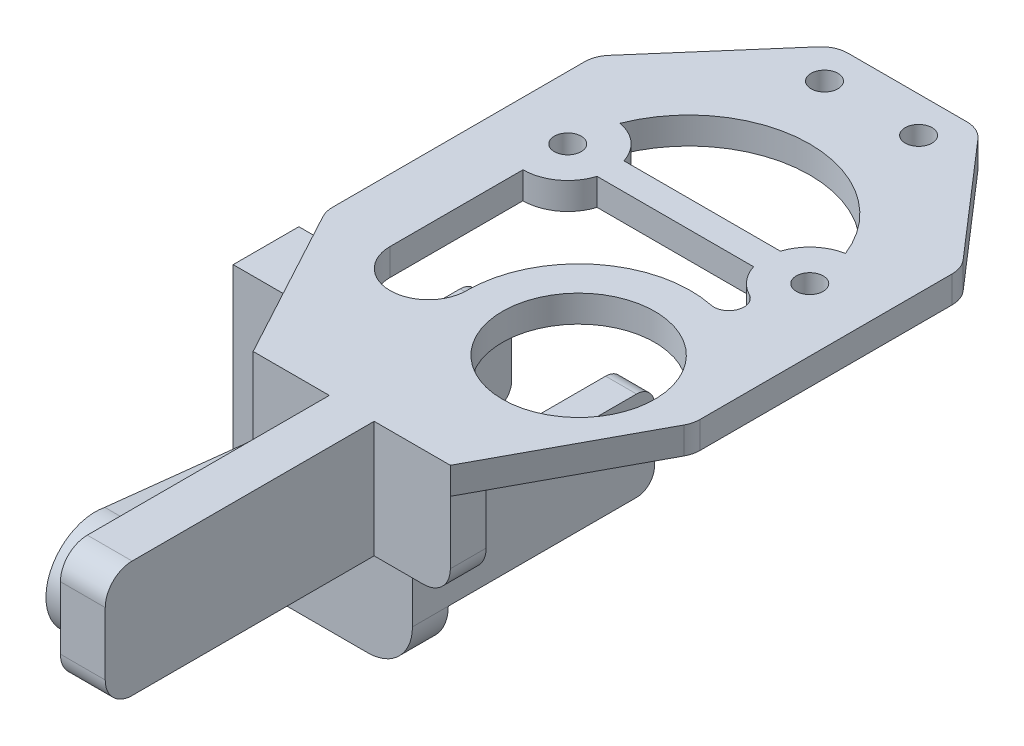
SolidWorks part; units mm, degrees
ref_plane "Front" through (0, 0, 0) normal (0, 0, 1) x (1, 0, 0)
ref_plane "Top" through (0, 0, 0) normal (0, 1, 0) x (1, 0, 0)
ref_plane "Right" through (0, 0, 0) normal (1, 0, 0) x (0, 0, -1)
sketch "Sketch1" plane through (0, 0, 0) normal (0, 1, 0) x (1, 0, 0)
  line L0 (0, 24.4003) -> (0, 0) construction
  line L1 (0, 0) -> (-13.5, 0) construction
  line L2 (8, 24.4003) -> (-8, 24.4003)
  line L3 (-8, 24.4003) -> (-20.5, 10)
  line L4 (-20.5, 10) -> (-20.5, -20)
  line L5 (-20.5, -20) -> (-11, -37.5997)
  line L6 (-11, -37.5997) -> (11, -37.5997)
  line L7 (20.5, -20) -> (11, -37.5997)
  line L8 (20.5, 10) -> (20.5, -20)
  line L9 (8, 24.4003) -> (20.5, 10)
  line L11 (7.5302, -19.8174) -> (17.65, -25.2799) construction
  line L12 (-13.5, -5) -> (-13.5, -19.8174)
  line L13 (8.7303, -1.5) -> (-8.7303, -1.5)
  line L15 (8.7303, 1.5) -> (-8.7303, 1.5)
  line L17 (8.7303, -1.5) -> (-8.7303, 1.5) construction
  line L18 (8.7303, 1.5) -> (-8.7303, -1.5) construction
  arc A0 (12.5741, 4.9135) -> (-12.5741, 4.9135) centre (0, 0) ccw
  circle A1 centre (-5.25, 20.3945) radius 1.5
  circle A4 centre (5.25, 20.3945) radius 1.5
  arc A5 (-13.5, -5) -> (-8.7303, -1.5) centre (-13.5, 0) ccw
  arc A6 (8.7303, -1.5) -> (11.188, -4.4333) centre (13.5, 0) ccw
  circle A7 centre (-13.5, 0) radius 1.5
  circle A8 centre (13.5, 0) radius 1.5
  arc A9 (-13.5, -19.8174) -> (-4.9698, -19.8174) centre (-9.2349, -19.8174) ccw
  arc A10 (-4.9698, -19.8174) -> (10.0668, -7.5775) centre (7.5302, -19.8174) cw
  arc A11 (10.0668, -7.5775) -> (11.188, -4.4333) centre (10.4088, -5.9275) ccw
  circle A12 centre (7.5302, -19.8174) radius 8.5
  arc A13 (-8.7303, 1.5) -> (-12.5741, 4.9135) centre (-13.5, 0) ccw
  arc A14 (12.5741, 4.9135) -> (8.7303, 1.5) centre (13.5, 0) ccw
  point P15 (0, -37.5997)
  dimension "D7" = 10.5
  dimension "D8" = 3
  dimension "D10" = 17
  dimension "D15" = 4
  dimension "D16" = 10
  dimension "D17" = 13.5
  dimension "D18" = 3
  dimension "D19" = 3
  dimension "D24" = 22
  dimension "D1" = 62
  dimension "D2" = 41
  dimension "D3" = 16
  dimension "D4" = 22
  dimension "D9" = 11.5
  dimension "D11" = 6
  dimension "D12" = 20
  dimension "D13" = 30
  dimension "D14" = 10
  dimension "D20" = 3
  dimension "D21" = 45
  dimension "D22" = 13.5
extrude "Boss-Extrude1" add sketch "Sketch1" along normal mid plane 3
fillet "Fillet1" radius 3 6 edges at (-20.5, 0, 20) (-20.5, 0, -10) (-8, 0, -24.4003) (8, 0, -24.4003) (20.5, 0, -10) (20.5, 0, 20)
sketch "Sketch4" plane through (0, -1.5, 0) normal (0, -1, 0) x (1, 0, 0)
  line L0 (-13.5, 1.5) -> (-13.5, 25.3259)
  line L2 (-23.5, 23.3259) -> (-3.5, 23.3259)
  line L3 (-23.5, 23.3259) -> (-23.5, 27.3259)
  line L4 (-23.5, 27.3259) -> (-3.5, 27.3259)
  line L5 (-3.5, 23.3259) -> (-3.5, 27.3259)
  line L6 (-23.5, 23.3259) -> (-3.5, 27.3259) construction
  line L7 (-23.5, 27.3259) -> (-3.5, 23.3259) construction
  circle A0 centre (-13.5, 0) radius 1.5 construction
  dimension "D1" = 20
  dimension "D2" = 4
extrude "Boss-Extrude2" add sketch "Sketch4" along normal blind 30
sketch "Sketch5" plane through (0, 0, 23.3259) normal (0, 0, -1) x (-1, 0, 0)
  line L0 (23.5, -31.5) -> (11.6601, -31.5) construction
  line L1 (11.6601, -1.5) -> (14.7975, -1.5)
  line L2 (11.6601, -1.5) -> (11.6601, -31.5)
  line L3 (11.6601, -31.5) -> (14.7975, -31.5)
sketch "Sketch7" plane through (0, -1.5, 0) normal (0, -1, 0) x (1, 0, 0)
  line L0 (-13.5, 0) -> (-7.25, 0)
  line L1 (-13.5, 0) -> (-19.75, 0)
  line L2 (-6.8097, 23.3259) -> (-3.5, 23.3259) construction
  line L3 (-7.25, 0) -> (-3.5, 0)
  line L4 (-7.25, 0) -> (-7.25, 23.3259)
  line L5 (-7.25, 23.3259) -> (-3.5, 23.3259)
  line L6 (-3.5, 0) -> (-3.5, 23.3259)
  line L8 (-19.75, 0) -> (-23.5, 0)
  line L9 (-19.75, 0) -> (-19.75, 23.3259)
  line L10 (-19.75, 23.3259) -> (-23.5, 23.3259)
  line L11 (-23.5, 0) -> (-23.5, 23.3259)
extrude "Boss-Extrude4" add sketch "Sketch7" along normal blind 25 contours L9 L8 L11 L10
sketch "Sketch10" plane through (0, 0, 23.3259) normal (0, 0, -1) x (-1, 0, 0)
  line L1 (3.5, -1.5) -> (6.95, -1.5)
  line L2 (3.5, -1.5) -> (3.5, -26.5)
  line L3 (3.5, -26.5) -> (6.95, -26.5)
  line L4 (6.95, -1.5) -> (6.95, -26.5)
  dimension "D1" = 3.45
  dimension "D2" = 25
extrude "Boss-Extrude15" add sketch "Sketch10" along normal blind 23
sketch "Sketch11" plane through (0, 0, 0) normal (0, 0, -1) x (-1, 0, 0)
  line L0 (19.75, -26.5) -> (19.75, -1.5) construction
  line L1 (23.5, -1.5) -> (19.75, -1.5)
  line L2 (23.5, -1.5) -> (23.5, -16.5)
  line L3 (23.5, -16.5) -> (19.75, -16.5)
  line L4 (19.75, -1.5) -> (19.75, -16.5)
  dimension "D1" = 15
extrude "Cut-Extrude1" cut sketch "Sketch11" against normal blind 20
sketch "Sketch12" plane through (0, 0, 0.3259) normal (0, 0, -1) x (-1, 0, 0)
  line L0 (3.5, -1.5) -> (3.5, -26.5) construction
  line L1 (6.95, -1.5) -> (3.5, -1.5)
  line L2 (6.95, -1.5) -> (6.95, -16.5)
  line L3 (6.95, -16.5) -> (3.5, -16.5)
  line L4 (3.5, -1.5) -> (3.5, -16.5)
  dimension "D1" = 15
extrude "Cut-Extrude2" cut sketch "Sketch12" against normal blind 20
sketch "Sketch13" plane through (0, -1.5, 0) normal (0, -1, 0) x (1, 0, 0)
  line L1 (11, 37.5997) -> (-11, 37.5997)
  line L2 (11, 37.5997) -> (11, 33.5997)
  line L3 (11, 33.5997) -> (-11, 33.5997)
  line L4 (-11, 37.5997) -> (-11, 33.5997)
  dimension "D1" = 4
extrude "Boss-Extrude16" add sketch "Sketch13" along normal blind 10
sketch "Sketch14" plane through (0, 0, 37.5997) normal (0, 0, 1) x (1, 0, 0)
  line L0 (0, -11.5) -> (0, 1.5)
  line L1 (11, -11.5) -> (-11, -11.5) construction
  line L2 (-11, 1.5) -> (11, 1.5) construction
  line L4 (-2.5, 1.5) -> (2.5, 1.5)
  line L5 (-2.5, 1.5) -> (-2.5, -11.5)
  line L6 (-2.5, -11.5) -> (2.5, -11.5)
  line L7 (2.5, 1.5) -> (2.5, -11.5)
  line L8 (-2.5, 1.5) -> (2.5, -11.5) construction
  line L9 (-2.5, -11.5) -> (2.5, 1.5) construction
  point P6 (0, -5)
  line M7 (-11, -11.5) -> (11, -11.5)
  line M10 (11, 1.5) -> (-11, 1.5)
  dimension "D1" = 5
extrude "Boss-Extrude17" add sketch "Sketch14" along normal blind 30 contours L7 L0 M10 M7 | L5 L0 M10 M7
fillet "Fillet3" radius 3 1 edges at (-11, -11.5, 35.5997)
fillet "Fillet4" radius 3 1 edges at (11, -11.5, 35.5997)
fillet "Fillet5" radius 3 1 edges at (0, 1.5, 67.5997)
fillet "Fillet6" radius 3 1 edges at (0, -11.5, 67.5997)
fillet "Fillet7" radius 2 1 edges at (-21.625, -16.5, 0)
fillet "Fillet8" radius 2 1 edges at (-21.625, -26.5, 0)
fillet "Fillet9" radius 2 1 edges at (-5.225, -26.5, 0.3259)
fillet "Fillet10" radius 2 1 edges at (-5.225, -16.5, 0.3259)
fillet "Fillet11" radius 5 3 edges at (-3.5, -29, 23.3259) (-5.1548, -31.5, 23.3259) (-3.5, -31.5, 25.3259)
fillet "Fillet12" radius 5 2 edges at (-23.5, -31.5, 25.3259) (-23.5, -29, 23.3259)
sketch "Sketch15" plane through (-2.5, 0, 0) normal (-1, 0, 0) x (0, 0, 1)
  line L0 (60.2185, -8.6736) -> (44.1642, -7.5644)
  line L1 (44.1642, -3.4644) -> (60.7012, -1.6869) construction
  line L2 (44.0391, -1.4663) -> (60.4874, 0.3016) construction
  line L3 (44.1642, -3.4644) -> (59.9553, -1.7671)
  line L6 (60.0195, -10.6646) -> (44.0836, -9.5636)
  line L7 (44.0391, -1.4663) -> (59.647, 0.2113)
  line L8 (60.7012, -8.7069) -> (44.1642, -7.5644) construction
  line L9 (60.5633, -10.7022) -> (44.0836, -9.5636) construction
  arc A2 (60.2185, -8.6736) -> (59.9553, -1.7671) centre (60.7012, -5.1969) ccw
  arc A3 (44.1642, -3.4644) -> (44.1642, -7.5644) centre (44.1642, -5.5144) ccw
  arc A4 (60.0195, -10.6646) -> (59.647, 0.2113) centre (60.7012, -5.1969) ccw
  arc A5 (59.9434, -10.6546) -> (59.5303, 0.1872) centre (60.7012, -5.1969) ccw construction
  arc A7 (44.0391, -1.4663) -> (44.0836, -9.5636) centre (44.1642, -5.5144) ccw
  dimension "D1" = 2
  dimension "D2" = 2
extrude "Boss-Extrude18" add sketch "Sketch15" along normal blind 3 contours L3 A2 L0 A3 | L6 A7 L7 A4
